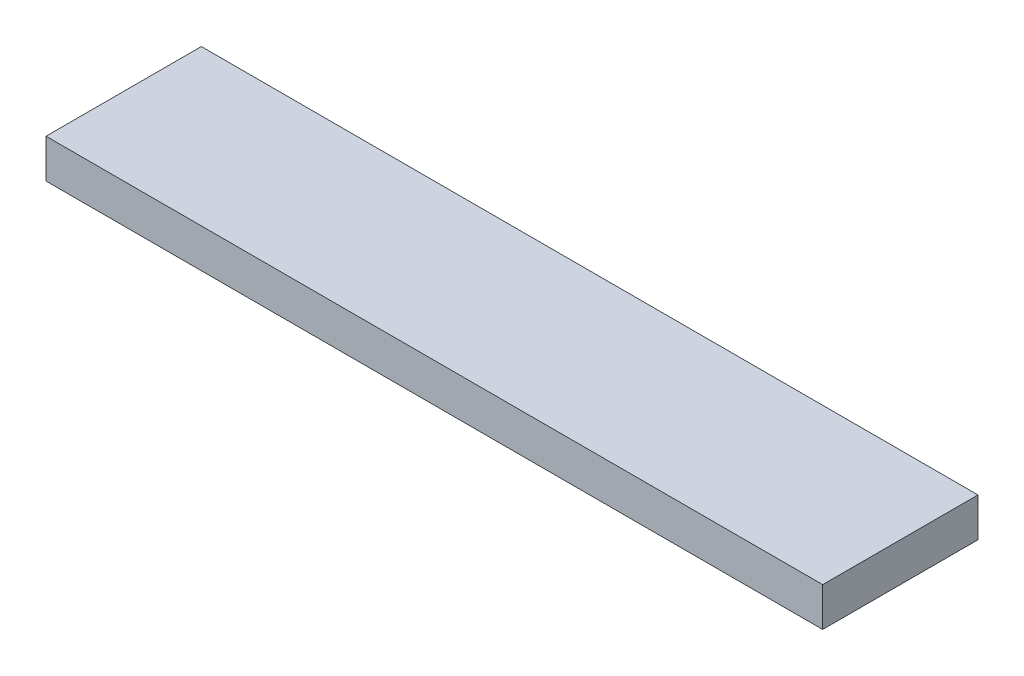
SolidWorks part; units mm, degrees
ref_plane "Front Plane" through (0, 0, 0) normal (0, 0, 1) x (1, 0, 0)
ref_plane "Top Plane" through (0, 0, 0) normal (0, 1, 0) x (1, 0, 0)
ref_plane "Right Plane" through (0, 0, 0) normal (1, 0, 0) x (0, 0, -1)
sketch "Sketch1" plane through (0, 0, 0) normal (0, 1, 0) x (1, 0, 0)
  line L1 (-63.5, -12.7) -> (63.5, -12.7)
  line L2 (-63.5, -12.7) -> (-63.5, 12.7)
  line L3 (-63.5, 12.7) -> (63.5, 12.7)
  line L4 (63.5, -12.7) -> (63.5, 12.7)
  line L5 (-63.5, -12.7) -> (63.5, 12.7) construction
  line L6 (-63.5, 12.7) -> (63.5, -12.7) construction
  point P0 (0, 0)
  dimension "D1" = 25.4
  dimension "D2" = 127
extrude "Boss-Extrude1" add sketch "Sketch1" along normal blind 6.35
